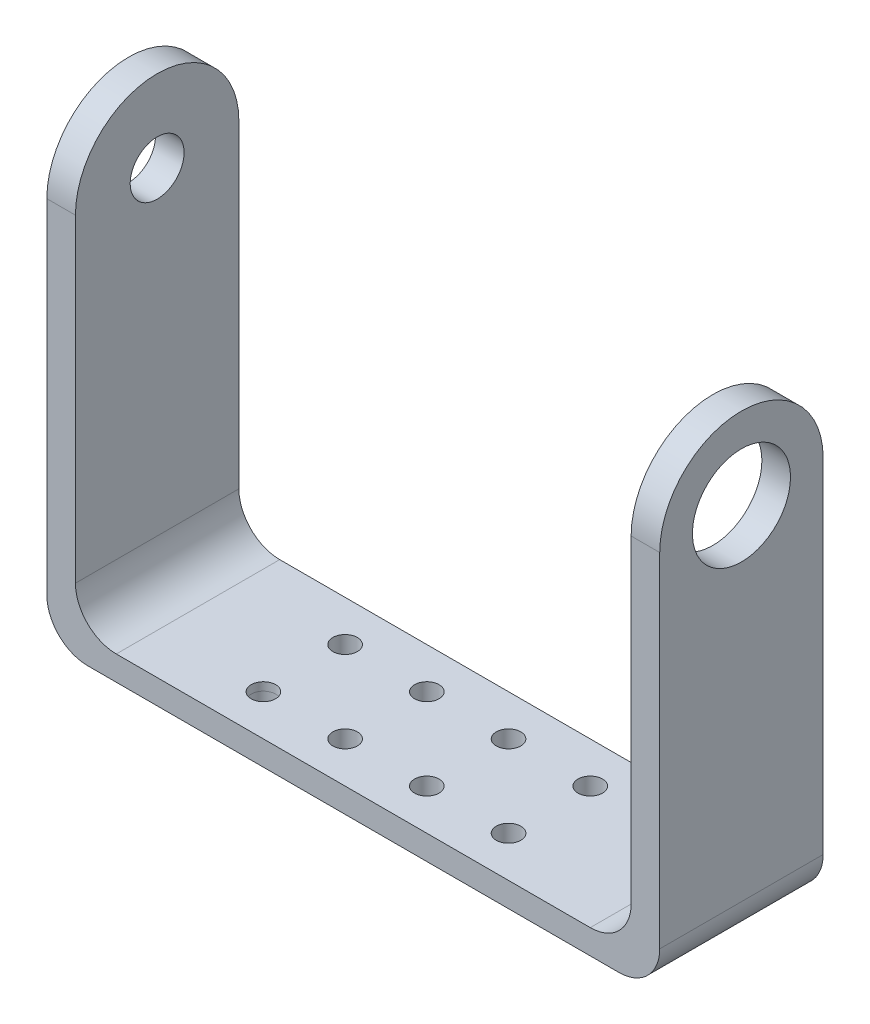
SolidWorks part; units mm, degrees
ref_plane "정면" through (0, 0, 0) normal (0, 0, 1) x (1, 0, 0)
ref_plane "윗면" through (0, 0, 0) normal (0, 1, 0) x (1, 0, 0)
ref_plane "우측면" through (0, 0, 0) normal (1, 0, 0) x (0, 0, -1)
sketch "스케치2" plane through (0, 0, 0) normal (0, 1, 0) x (1, 0, 0)
  line L0 (0, 10) -> (0, -10) construction
  line L1 (35, -10) -> (-35, -10)
  line L3 (35, 10) -> (-35, 10)
  line L4 (-35, -10) -> (-35, 10)
  line L5 (35, -10) -> (-35, 10) construction
  line L6 (35, 10) -> (-35, -10) construction
  line L8 (35, 10) -> (38.5, 10)
  line L10 (35, -10) -> (38.5, -10)
  line L11 (38.5, 10) -> (38.5, -10)
  circle A0 centre (-15, 5) radius 1.5
  circle A1 centre (-5, 5) radius 1.5
  circle A2 centre (-15, -5) radius 1.5
  circle A3 centre (-5, -5) radius 1.5
  circle A4 centre (15, -5) radius 1.5
  circle A5 centre (5, -5) radius 1.5
  circle A6 centre (5, 5) radius 1.5
  circle A7 centre (15, 5) radius 1.5
  point P0 (0, 0)
  point P6 (-15, 5)
  point P7 (-5, 5)
  point P8 (-15, -5)
  point P9 (-5, -5)
  dimension "D9" = 5
  dimension "D1" = 70
  dimension "D2" = 20
  dimension "D3" = 3.5
  dimension "D4" = 5
  dimension "D5" = 10
  dimension "D6" = 5
  dimension "D7" = 10
  dimension "D8" = 10
extrude "보스-돌출1" add sketch "스케치2" along normal blind 2
ref_plane "평면1" through (0, 2, 0) normal (0, 1, 0) x (1, 0, 0)
sketch "스케치3" plane through (0, 2, 0) normal (0, 1, 0) x (1, 0, 0)
  line L0 (-35, -10) -> (38.5, -10) construction
  line L1 (-35, 10) -> (-33, 10)
  line L2 (-35, 10) -> (-35, -10)
  line L3 (-35, -10) -> (-33, -10)
  line L4 (-33, 10) -> (-33, -10)
  line L5 (-35, -10) -> (38.5, -10) construction
  line L6 (38.5, 10) -> (35, 10)
  line L7 (38.5, 10) -> (38.5, -10)
  line L8 (38.5, -10) -> (35, -10)
  line L9 (35, 10) -> (35, -10)
  dimension "D1" = 2
  dimension "D2" = 3.5
extrude "보스-돌출2" add sketch "스케치3" along normal blind 55
ref_plane "평면2" through (38.5, 0, 0) normal (1, 0, 0) x (0, 0, -1)
ref_plane "평면3" through (-35, 0, 0) normal (-1, 0, 0) x (0, 0, 1)
sketch "스케치9" plane through (38.5, 0, 0) normal (1, 0, 0) x (0, 0, -1)
  line L0 (-10, 57) -> (10, 57) construction
  line L1 (-10, 57) -> (-10, 0) construction
  line L4 (-10, 47) -> (-10, 57)
  line L5 (-10, 57) -> (10, 57)
  line L6 (10, 57) -> (10, 47)
  line L7 (-10, 47) -> (10, 47) construction
  arc A2 (10, 47) -> (-10, 47) centre (0, 47) ccw
  circle A3 centre (0, 47) radius 6
  point P10 (0, 47)
  point P17 (0, 54.07)
  point P18 (-7.07, 47)
  point P19 (0, 47)
  dimension "D6" = 12
  dimension "D4" = 7.07
  dimension "D5" = 7.07
extrude "컷-돌출1" cut sketch "스케치9" against normal blind 87 contours A2 L6 L5 | A2 L5 L4 | L7 A3 | A3 L7
sketch "스케치7" plane through (-35, 0, 0) normal (-1, 0, 0) x (0, 0, 1)
  circle A0 centre (0, 47) radius 6
  circle A1 centre (0, 47) radius 3.3
extrude "보스-돌출3" add sketch "스케치7" against normal blind 2
ref_plane "평면4" through (0, 0, 0) normal (0, -1, 0) x (-1, 0, 0)
ref_plane "평면5" through (-35, 0, 0) normal (-1, 0, 0) x (0, 0, 1)
sketch "스케치10" plane through (-35, 0, 0) normal (-1, 0, 0) x (0, 0, 1)
  line L0 (10, 0) -> (-10, 0)
  line L1 (-11, 0) -> (11, 0) construction
  line L2 (10, 47) -> (10, 0) construction
  line L3 (-10, 47) -> (-10, 0) construction
  line L4 (-10, 0) -> (-10, 47)
  line L6 (10, 47) -> (10, 0)
  arc A0 (-10, 47) -> (10, 47) centre (0, 47) cw
  circle A1 centre (0, 47) radius 3.3
extrude "보스-돌출4" add sketch "스케치10" along normal blind 1.5 contours A0 L4 L0 L6 A1
ref_plane "평면6" through (0, 2, 0) normal (0, 1, 0) x (1, 0, 0)
sketch "스케치11" plane through (0, 2, 0) normal (0, 1, 0) x (1, 0, 0)
  line L1 (-33, -10) -> (35, -10)
  line L2 (-33, -10) -> (-33, 10)
  line L3 (-33, 10) -> (35, 10)
  line L4 (35, -10) -> (35, 10)
  circle A0 centre (-15, 5) radius 1.5
  circle A1 centre (-5, 5) radius 1.5
  circle A2 centre (5, 5) radius 1.5
  circle A3 centre (15, 5) radius 1.5
  circle A4 centre (15, -5) radius 1.5
  circle A5 centre (5, -5) radius 1.5
  circle A6 centre (-5, -5) radius 1.5
  circle A7 centre (-15, -5) radius 1.4989
  dimension "D1" = 3
extrude "보스-돌출5" add sketch "스케치11" along normal blind 1
fillet "필렛6" radius 5 1 edges at (-33, 3, 0)
fillet "필렛7" radius 5 1 edges at (35, 3, 0)
fillet "필렛8" radius 5 2 edges at (38.5, 0, 0) (-36.5, 0, 0)
